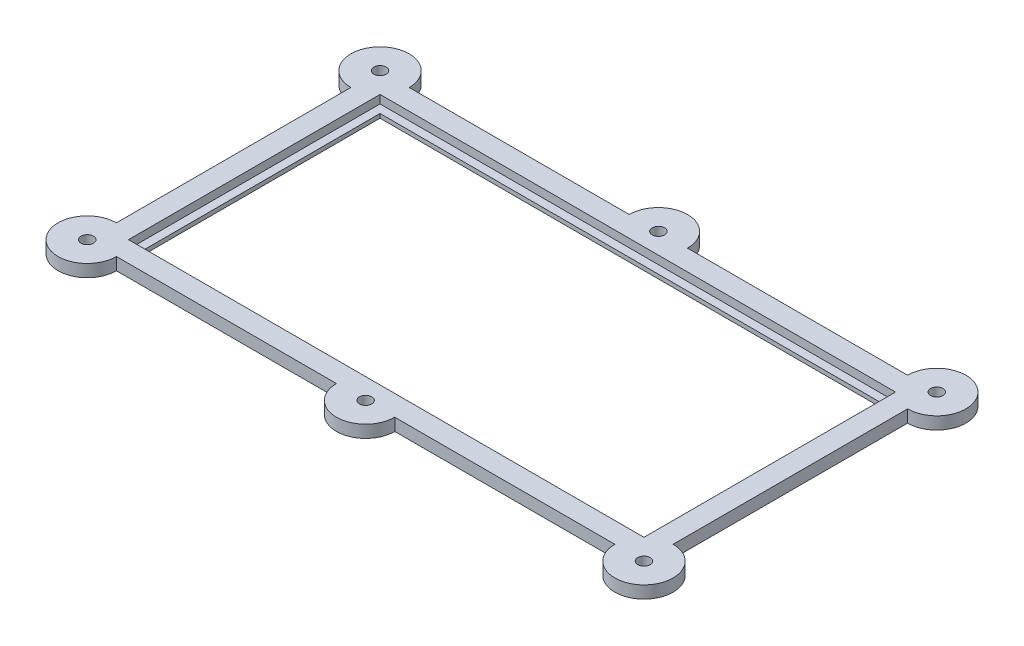
SolidWorks part; units mm, degrees
ref_plane "Front Plane" through (0, 0, 0) normal (0, 0, 1) x (1, 0, 0)
ref_plane "Top Plane" through (0, 0, 0) normal (0, 1, 0) x (1, 0, 0)
ref_plane "Right Plane" through (0, 0, 0) normal (1, 0, 0) x (0, 0, -1)
sketch "Sketch1" plane through (0, 0, 0) normal (0, 1, 0) x (1, 0, 0)
  line L0 (31.25, 15.25) -> (33.75, 17.75) construction
  line L1 (31.25, -15.25) -> (-31.25, -15.25)
  line L2 (31.25, -15.25) -> (31.25, 15.25)
  line L3 (31.25, 15.25) -> (-31.25, 15.25)
  line L4 (-31.25, -15.25) -> (-31.25, 15.25)
  line L5 (31.25, -15.25) -> (-31.25, 15.25) construction
  line L6 (31.25, 15.25) -> (-31.25, -15.25) construction
  line L7 (33.75, -17.75) -> (-33.75, -17.75)
  line L8 (33.75, -17.75) -> (33.75, 17.75)
  line L9 (33.75, 17.75) -> (-33.75, 17.75)
  line L10 (-33.75, -17.75) -> (-33.75, 17.75)
  line L11 (31.25, -15.25) -> (33.75, -17.75) construction
  line L12 (-31.25, 15.25) -> (-33.75, 17.75) construction
  line L13 (-31.25, 15.25) -> (-33.75, 15.25) construction
  line L14 (-31.25, 15.25) -> (-31.25, 17.75) construction
  point P0 (0, 0)
  point P6 (0, 0)
  dimension "D1" = 2.5
  dimension "D2" = 30.5
  dimension "D3" = 62.5
extrude "Boss-Extrude1" add sketch "Sketch1" along normal blind 1
sketch "Sketch2" plane through (0, 0, 0) normal (0, -1, 0) x (1, 0, 0)
  line L0 (33.75, -17.75) -> (-33.75, -17.75) construction
  line L1 (-33.75, -17.75) -> (-33.75, 17.75) construction
  line L2 (-33.75, 17.75) -> (33.75, 17.75) construction
  line L3 (33.75, 17.75) -> (33.75, -17.75) construction
  line L4 (33.75, -17.75) -> (-33.75, -17.75)
  line L5 (-33.75, -17.75) -> (-33.75, 17.75)
  line L6 (-33.75, 17.75) -> (33.75, 17.75)
  line L7 (33.75, 17.75) -> (33.75, -17.75)
  line L8 (-31.25, -15.25) -> (-31.25, 15.25) construction
  line L9 (30.25, -14.25) -> (-30.25, -14.25)
  line L10 (30.25, -14.25) -> (30.25, 14.25)
  line L11 (30.25, 14.25) -> (-30.25, 14.25)
  line L12 (-30.25, -14.25) -> (-30.25, 14.25)
  line L13 (30.25, -14.25) -> (-30.25, 14.25) construction
  line L14 (30.25, 14.25) -> (-30.25, -14.25) construction
  line L15 (-31.25, 15.25) -> (31.25, 15.25) construction
  point P2 (0, 0)
  dimension "D1" = 1
  dimension "D2" = 1
extrude "Boss-Extrude2" add sketch "Sketch2" along normal blind 0.5
sketch "Sketch3" plane through (0, 1, 0) normal (0, 1, 0) x (1, 0, 0)
  line L0 (33.75, 17.75) -> (-33.75, 17.75) construction
  line L1 (-33.75, -17.75) -> (33.75, -17.75) construction
  line L2 (-3.5355, 17.75) -> (3.5355, 17.75)
  line L3 (-3.5355, -17.75) -> (3.5355, -17.75)
  circle A0 centre (-33.75, 17.75) radius 3.5355
  circle A1 centre (33.75, 17.75) radius 3.5355
  circle A2 centre (33.75, -17.75) radius 3.5355
  circle A3 centre (-33.75, -17.75) radius 3.5355
  arc A4 (3.5355, 17.75) -> (-3.5355, 17.75) centre (0, 17.75) ccw
  arc A5 (-3.5355, -17.75) -> (3.5355, -17.75) centre (0, -17.75) ccw
extrude "Boss-Extrude3" add sketch "Sketch3" against normal up to surface (1.5 mm away) up to face at (0, -0.5, 0)
sketch "Sketch4" plane through (0, 1, 0) normal (0, 1, 0) x (1, 0, 0)
  circle A0 centre (-33.75, 17.75) radius 0.75
  circle A1 centre (33.75, 17.75) radius 0.75
  circle A2 centre (33.75, -17.75) radius 0.75
  circle A3 centre (-33.75, -17.75) radius 0.75
  circle A4 centre (0, 17.75) radius 0.75
  circle A5 centre (0, -17.75) radius 0.75
  dimension "D1" = 1.5
extrude "Cut-Extrude1" cut sketch "Sketch4" against normal through all both and the other way through all
